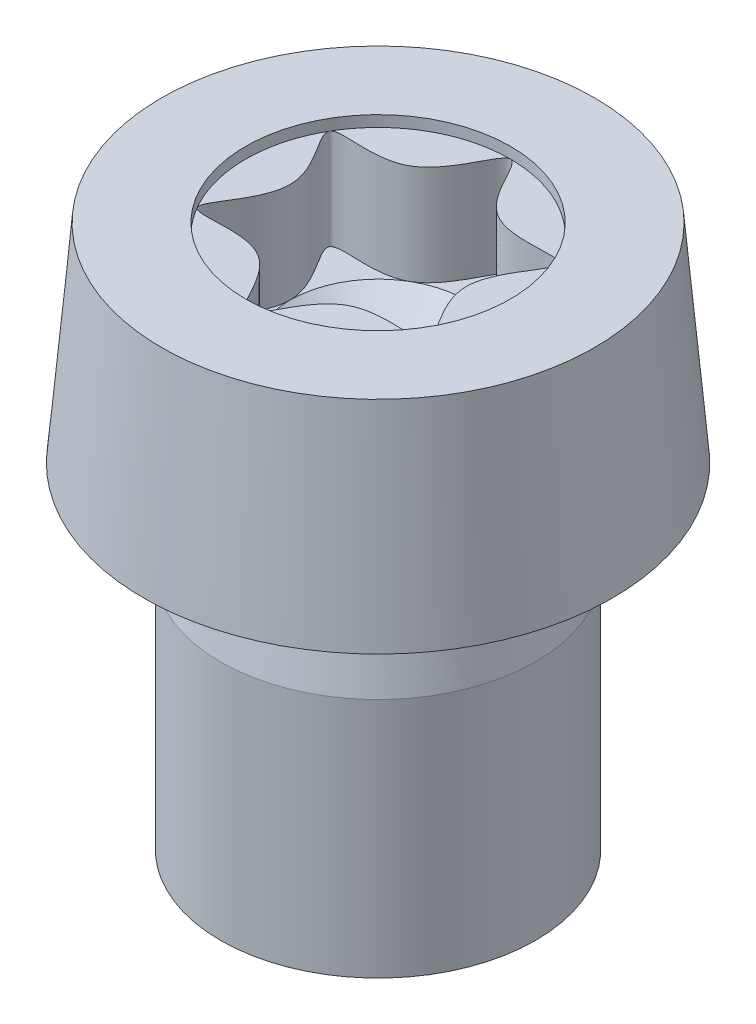
SolidWorks part; units mm, degrees
ref_plane "Front" through (0, 0, 0) normal (0, 0, 1) x (1, 0, 0)
ref_plane "Top" through (0, 0, 0) normal (0, 1, 0) x (1, 0, 0)
ref_plane "Right" through (0, 0, 0) normal (1, 0, 0) x (0, 0, -1)
sketch "Sketch1" plane through (0, 0, 0) normal (0, 0, 1) x (1, 0, 0)
  line L0 (0, 0) -> (0, 5.1006) construction
  line L1 (0, 8.1) -> (3.2288, 8.1)
  line L2 (3.2288, 8.1) -> (3.5, 5)
  line L3 (3.5, 5) -> (2.35, 5)
  line L4 (2.35, 0) -> (2.35, 3.6)
  line L5 (2.35, 0) -> (0, 0)
  line L6 (0, 0) -> (0, 8.1)
  line L7 (3.5, 5) -> (3.5, 4.3) construction
  line L8 (2.35, 3.6) -> (2.07, 5)
  line L9 (2.07, 5) -> (2.35, 5)
  line L10 (3.5, 4.3) -> (3.5, 0.7) construction
  dimension "length" = 5
  dimension "head_ht" = 3.1
  dimension "head_dia" = 7
  dimension "dia" = 4.7
  dimension "D1" = 5
  dimension "pitch" = 0.7
  dimension "thread_gap" = 1.4
  dimension "D2" = 0.28
  dimension "thread_length" = 3.6
revolve "Body-Revolve" add sketch "Sketch1" angle 360 about L0
cosmetic thread "ThreadCosmetic" [suppressed] parameters "D1"=3.6, "D2"=3.9423
fillet "Fillet1" radius 0.2 1 edges at (0, 5, -2.07)
sketch "Sketch2" plane through (0, 8.1, 0) normal (0, 1, 0) x (-1, 0, 0)
  line L0 (0, -2.1725) -> (0, 0)
  line L1 (0, 0) -> (-0.9875, -1.7104)
  circle A0 centre (0, 0) radius 1.975
  circle A1 centre (0, 0) radius 1.3167
  spline S0 degree 3 poles (0.426, -0.7378) (0, -2.5936) (-0.426, -0.7378) (-2.2461, -1.2968) (-0.8519, 0) (-2.2461, 1.2968) (-0.426, 0.7378) (0, 2.5936) (0.426, 0.7378) (2.2461, 1.2968) (0.8519, 0) (2.2461, -1.2968) (0.426, -0.7378) (0, -2.5936) (-0.426, -0.7378) knots -0.25 -0.166667 -0.083333 0 0.083333 0.166667 0.25 0.333333 0.416667 0.5 0.583333 0.666667 0.75 0.833333 0.916667 1 1.083333 1.166667 1.25 only from (0, -1.975) to (0, -1.975)
  point P5 (0, -1.975)
  point P7 (-0.6583, -1.1403)
  point P10 (-1.7104, -0.9875)
  point P11 (-1.7104, 0.9875)
  point P12 (0, 1.975)
  point P13 (1.7104, 0.9875)
  point P14 (1.7104, -0.9875)
  point P15 (-1.3167, 0)
  point P16 (-0.6583, 1.1403)
  point P17 (0.6583, 1.1403)
  point P18 (1.3167, 0)
  point P19 (0.6583, -1.1403)
  dimension "socket_dia" = 3.95
  dimension "D1" = 2.6333
  dimension "D2" = 2.1725
  dimension "D3" = 30
extrude "Socket-Cut-Extrude1" cut sketch "Sketch2" against normal blind 1.66 contours S0
sketch "Sketch3" plane through (0, 8.1, 0) normal (0, 1, 0) x (-1, 0, 0)
  circle A0 centre (0, 0) radius 1.975
  dimension "D1" = 3.95
extrude "Socket-Cut-Extrude2" cut sketch "Sketch3" against normal blind 0.166
sketch "Sketch4" plane through (0, 0, 0) normal (0, 0, 1) x (1, 0, 0)
  line L0 (0, 6.44) -> (1.3167, 6.44)
  line L1 (1.7178, 6.44) -> (-1.7178, 6.44) construction
  line L2 (1.3167, 6.44) -> (0, 5.31)
  line L3 (0, 0) -> (0, 5.1006) construction
  line L4 (0, 5.31) -> (0, 6.44)
  line L5 (1.975, 8.1) -> (-1.975, 8.1) construction
  dimension "D1" = 2.79
  dimension "D2" = 1.3167
revolve "Drill-Cut-Revolve" cut sketch "Sketch4" angle 360 about axis through (0, 0, 0) along (0, 1, 0)
sketch "Sketch5" plane through (0, 0, 0) normal (0, 0, 1) x (1, 0, 0)
  line L0 (2.35, 0) -> (1.9711, 0.2187)
  line L1 (1.9711, 0.2187) -> (2.35, 0.4375)
  line L2 (2.35, 0) -> (2.35, 3.6) construction
  line L3 (2.35, 0.4375) -> (2.35, 0)
  line L4 (0, 0) -> (0, 5.1006) construction
  dimension "D1" = 1.9711
revolve "ThreadSchematic" [suppressed] cut sketch "Sketch5" angle 360 about axis through (0, 0, 0) along (0, 1, 0)
pattern_linear "ThdSchPat" [suppressed] count 5 spacing 0.7 along (0, 1, 0)
equation "\"D2@Sketch1\" = 0.2*\"thread_gap@Sketch1\""
equation "\"D1@Sketch2\" = \"socket_dia@Sketch2\" / 1.5"
equation "\"D2@Sketch2\" = \"socket_dia@Sketch2\" / 2 * 1.1"
equation "\"D1@Sketch3\" =\"socket_dia@Sketch2\""
equation "\"D1@Socket-Cut-Extrude2\" = .1 * \"socket_dep@Socket-Cut-Extrude1\""
equation "\"D1@Sketch4\" = 0.9*\"head_ht@Sketch1\""
equation "\"D2@Sketch4\" = \"D1@Sketch2\" / 2"
equation "\"D1@ThreadCosmetic\" = \"thread_length@Sketch1\""
equation "\"D2@ThreadCosmetic\" = \"dia@Sketch1\" - 1.0825 * \"pitch@Sketch1\""
equation "\"D1@Sketch5\" = \"D2@ThreadCosmetic\" / 2"
equation "\"D3@ThdSchPat\" = \"pitch@Sketch1\""
equation "\"D1@ThdSchPat\" = \"thread_length@Sketch1\" / \"pitch@Sketch1\""
